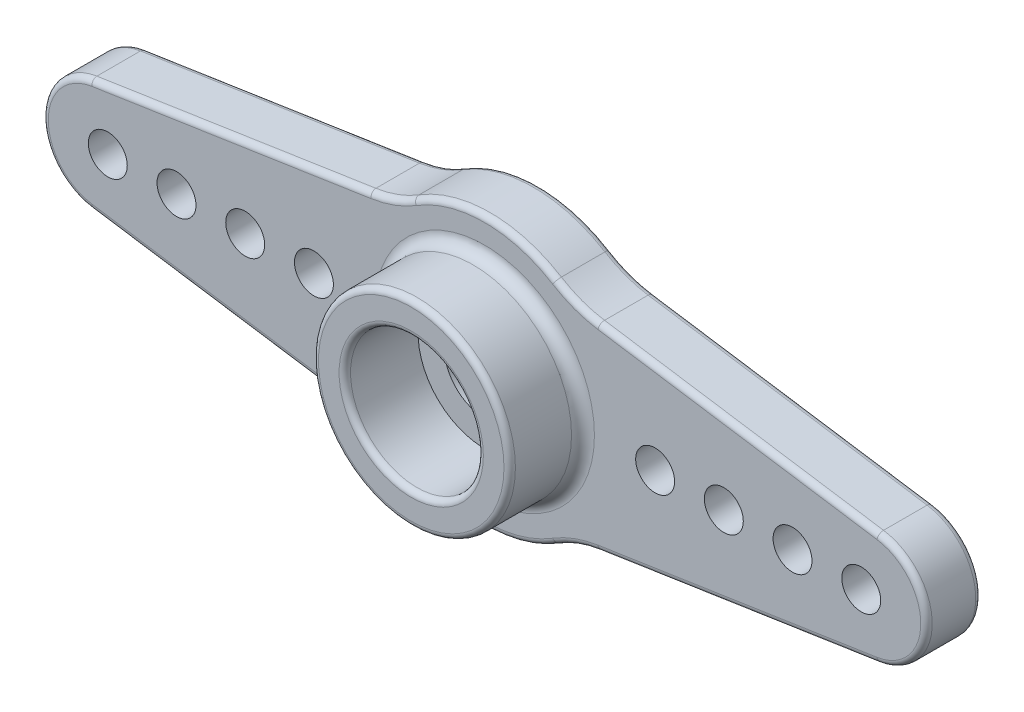
SolidWorks part; units mm, degrees
ref_plane "Front Plane" through (0, 0, 0) normal (0, 0, 1) x (1, 0, 0)
ref_plane "Top Plane" through (0, 0, 0) normal (0, 1, 0) x (1, 0, 0)
ref_plane "Right Plane" through (0, 0, 0) normal (1, 0, 0) x (0, 0, -1)
sketch "Sketch1" plane through (0, 0, 0) normal (0, 0, 1) x (1, 0, 0)
  line L0 (-4.9917, 4.3215) -> (-17.1753, 2.4717)
  line L1 (-17.1753, -2.4717) -> (-4.9917, -4.3215)
  line L2 (0, 0) -> (0, 9.7744) construction
  line L3 (0, 0) -> (-16.8, 0) construction
  line L4 (17.1753, -2.4717) -> (4.9917, -4.3215)
  line L5 (4.9917, 4.3215) -> (17.1753, 2.4717)
  arc A0 (-3.1082, -5.0149) -> (3.1082, -5.0149) centre (0, 0) ccw
  circle A1 centre (0, 0) radius 1.75
  arc A2 (-17.1753, 2.4717) -> (-17.1753, -2.4717) centre (-16.8, 0) ccw
  arc A3 (17.1753, 2.4717) -> (17.1753, -2.4717) centre (16.8, 0) cw
  arc A4 (3.1082, 5.0149) -> (-3.1082, 5.0149) centre (0, 0) ccw
  arc A5 (-4.9917, -4.3215) -> (-3.1082, -5.0149) centre (-5.7422, -9.2648) cw
  arc A6 (3.1082, -5.0149) -> (4.9917, -4.3215) centre (5.7422, -9.2648) cw
  arc A7 (4.9917, 4.3215) -> (3.1082, 5.0149) centre (5.7422, 9.2648) cw
  arc A8 (-3.1082, 5.0149) -> (-4.9917, 4.3215) centre (-5.7422, 9.2648) cw
  point P1 (0, 0)
  point P17 (-3.8158, -4.5)
  point P20 (3.8158, -4.5)
  point P23 (3.8158, 4.5)
  point P26 (-3.8158, 4.5)
  dimension "D1" = 11.8
  dimension "D2" = 3.5
  dimension "D3" = 2.5
  dimension "D6" = 5
  dimension "D4" = 33.6
  dimension "D5" = 9
extrude "Boss-Extrude1" add sketch "Sketch1" along normal blind 2.4
sketch "Sketch2" plane through (0, 0, 2.4) normal (0, 0, 1) x (1, 0, 0)
  circle A0 centre (0, 0) radius 4.3
  circle A1 centre (0, 0) radius 2.9
  dimension "D1" = 8.6
  dimension "D2" = 5.8
extrude "Boss-Extrude2" add sketch "Sketch2" along normal blind 3.2
sketch "Sketch4" plane through (0, 0, 0) normal (0, 0, -1) x (-1, 0, 0)
  circle A0 centre (0, 0) radius 3.3
  circle A1 centre (0, 0) radius 3.6
  dimension "D1" = 7.2
  dimension "D2" = 6.6
extrude "Boss-Extrude3" add sketch "Sketch4" along normal blind 0.2
sketch "Sketch5" plane through (0, 0, 0) normal (0, 0, -1) x (-1, 0, 0)
  circle A0 centre (0, 0) radius 3.3 construction
  circle A1 centre (0, 0) radius 3.3
  circle A2 centre (0, 0) radius 4
  circle A3 centre (0, 0) radius 3.6 construction
  circle A4 centre (0, 0) radius 3.6
  dimension "D1" = 8
extrude "Cut-Extrude2" cut sketch "Sketch5" against normal blind 0.4
sketch "Sketch6" plane through (0, 0, 0) normal (0, 0, -1) x (-1, 0, 0)
  line L0 (0, 0) -> (0, 1.0197) construction
  circle A1 centre (7.45, 0) radius 0.85
  point P1 (3.5, 7)
  point P4 (0, 0)
  point P5 (3.5, 1.0197)
  point P7 (0, 0)
  dimension "D1" = 1.7
  dimension "D2" = 7.45
extrude "Cut-Extrude3" cut sketch "Sketch6" against normal through all
pattern_linear "LPattern1" count 4 spacing 3 along (-1, 0, 0) of "Cut-Extrude3"
mirror "Mirror1" about plane through (0, 0, 0) normal (1, 0, 0) of "LPattern1", "Cut-Extrude3"
fillet "Fillet1" radius 0.25 26 edges at (4.3, 0, 5.6) (0, -5.9, 2.4) (0, -5.9, 0) (2.9, 0, 5.6) (-4.0148, -4.5727, 2.4) (-11.0835, -3.3966, 2.4) (-19.3, 0, 2.4) (-11.0835, 3.3966, 2.4) (-4.0148, 4.5727, 2.4) (0, 5.9, 2.4) (4.0148, 4.5727, 2.4) (11.0835, 3.3966, 2.4) (19.3, 0, 2.4) (11.0835, -3.3966, 2.4) (4.0148, -4.5727, 2.4) (-4.0148, -4.5727, 0) (-11.0835, -3.3966, 0) (-19.3, 0, 0) (-11.0835, 3.3966, 0) (-4.0148, 4.5727, 0) (0, 5.9, 0) (4.0148, 4.5727, 0) (11.0835, 3.3966, 0) (19.3, 0, 0) (11.0835, -3.3966, 0) (4.0148, -4.5727, 0)
fillet "Fillet2" radius 0.5 1 edges at (4.3, 0, 2.4)
